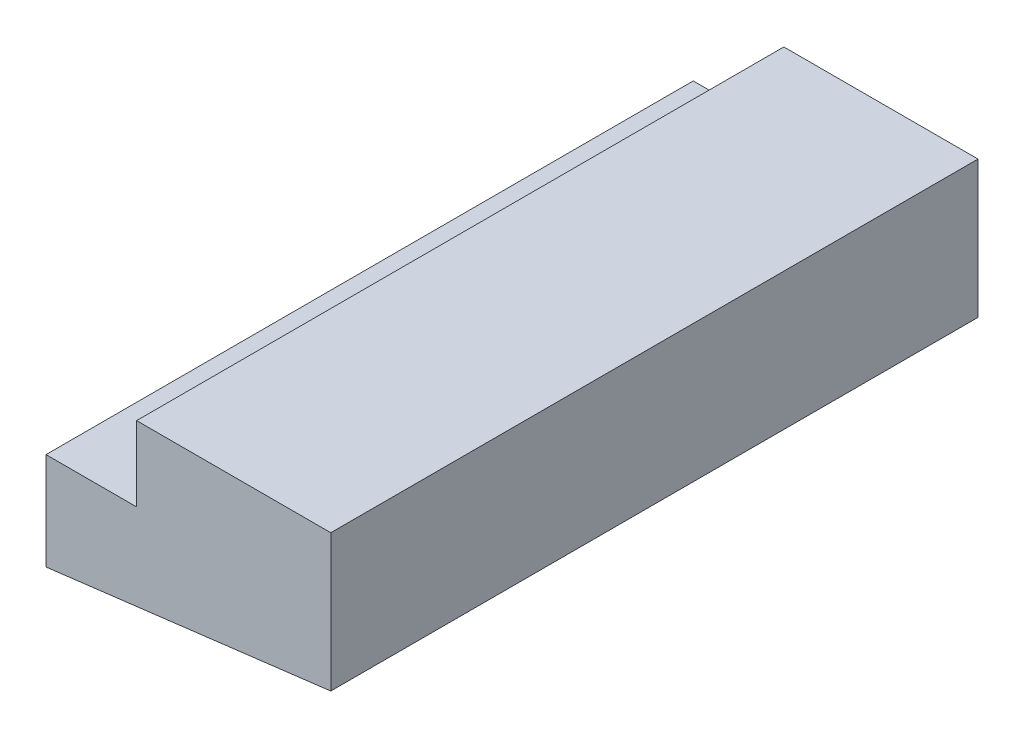
SolidWorks part; units mm, degrees
ref_plane "Front Plane" through (0, 0, 0) normal (0, 0, 1) x (1, 0, 0)
ref_plane "Top Plane" through (0, 0, 0) normal (0, 1, 0) x (1, 0, 0)
ref_plane "Right Plane" through (0, 0, 0) normal (1, 0, 0) x (0, 0, -1)
sketch "Sketch1" plane through (0, 0, 0) normal (0, 0, 1) x (1, 0, 0)
  line L0 (0, 0) -> (105, 0)
  line L1 (126.5, 0) -> (-126.5, 0) construction
  line L2 (105, 0) -> (105, -24)
  line L3 (105, -24) -> (70, -24)
  line L4 (70, -24) -> (70, -72)
  line L5 (70, -72) -> (50, -72)
  line L6 (50, -72) -> (50, 0)
  line L7 (0, -62.6555) -> (0, 62.6555) construction
  line L8 (50, -72) -> (0, -72)
  line L9 (25, -72) -> (25, -46.1199)
  circle A0 centre (0, -63.9192) radius 50
  dimension "D4" = 100
  dimension "D1" = 35
  dimension "D2" = 24
  dimension "D3" = 48
  dimension "D5" = 20
  dimension "D6" = 25
sketch "Sketch2" plane through (0, 0, 0) normal (0, 0, 1) x (1, 0, 0)
  line L1 (105, 0) -> (180, 0)
  line L2 (180, 0) -> (180, -52.9684)
  line L3 (180, -52.9684) -> (70, -66.4747)
  line L4 (105, 0) -> (105, -28.8726)
  line L5 (105, -28.8726) -> (70, -28.8726)
  line L6 (70, -24) -> (70, -72) construction
  line L7 (70, -28.8726) -> (70, -66.4747)
  line L9 (70, -72) -> (50, -72) construction
  line L10 (70, -66.4747) -> (25, -72) construction
  dimension "D1" = 75
  dimension "D2" = 110
  dimension "D3" = 7
extrude "Boss-Extrude1" add sketch "Sketch2" along normal blind 250
